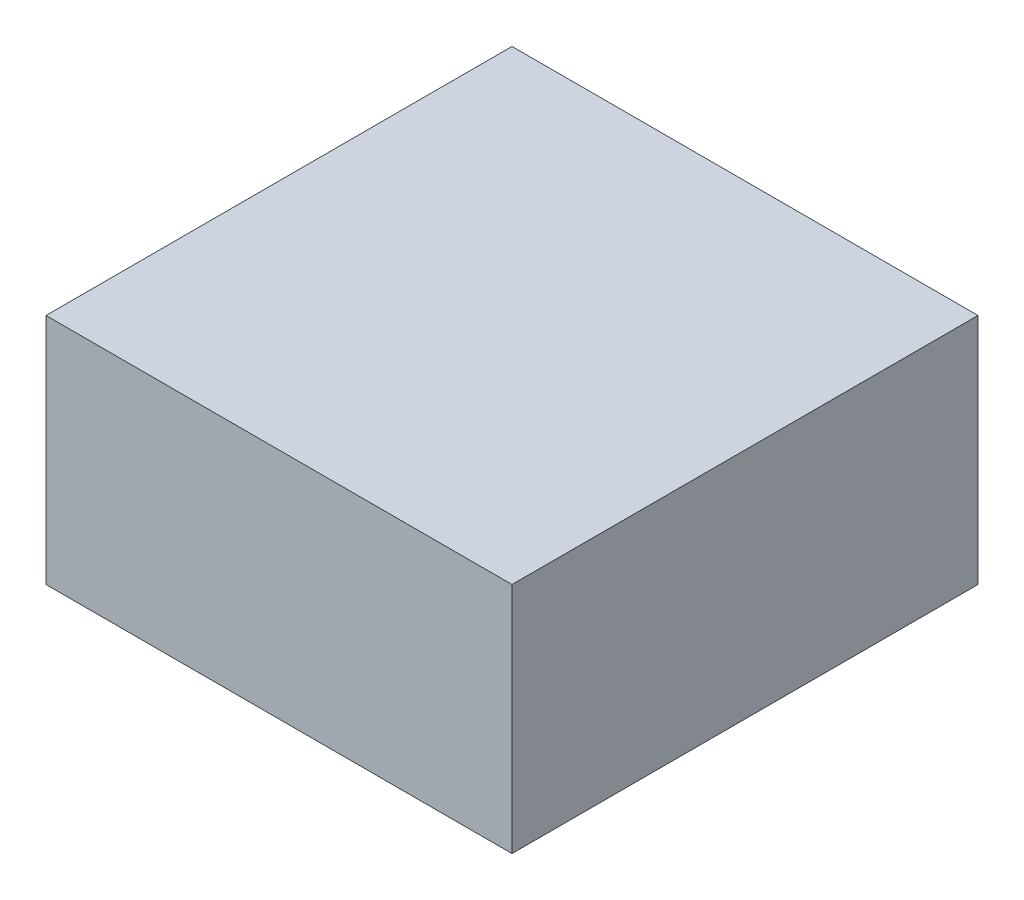
SolidWorks part; units mm, degrees
ref_plane "Ebene vorne" through (0, 0, 0) normal (0, 0, 1) x (1, 0, 0)
ref_plane "Ebene oben" through (0, 0, 0) normal (0, 1, 0) x (1, 0, 0)
ref_plane "Ebene rechts" through (0, 0, 0) normal (1, 0, 0) x (0, 0, -1)
sketch "Skizze1" plane through (0, 0, 0) normal (1, 0, 0) x (0, 0, -1)
  line L0 (0, -0.5) -> (0, 0.5) construction
  line L1 (-0.5, 0) -> (0.5, 0)
  line L2 (-0.5, 0) -> (-0.5, -0.5)
  line L3 (-0.5, -0.5) -> (0.5, -0.5)
  line L4 (0.5, 0) -> (0.5, -0.5)
  dimension "D1" = 1
extrude "Aufsatz-Linear austragen1" add sketch "Skizze1" along normal mid plane 1
